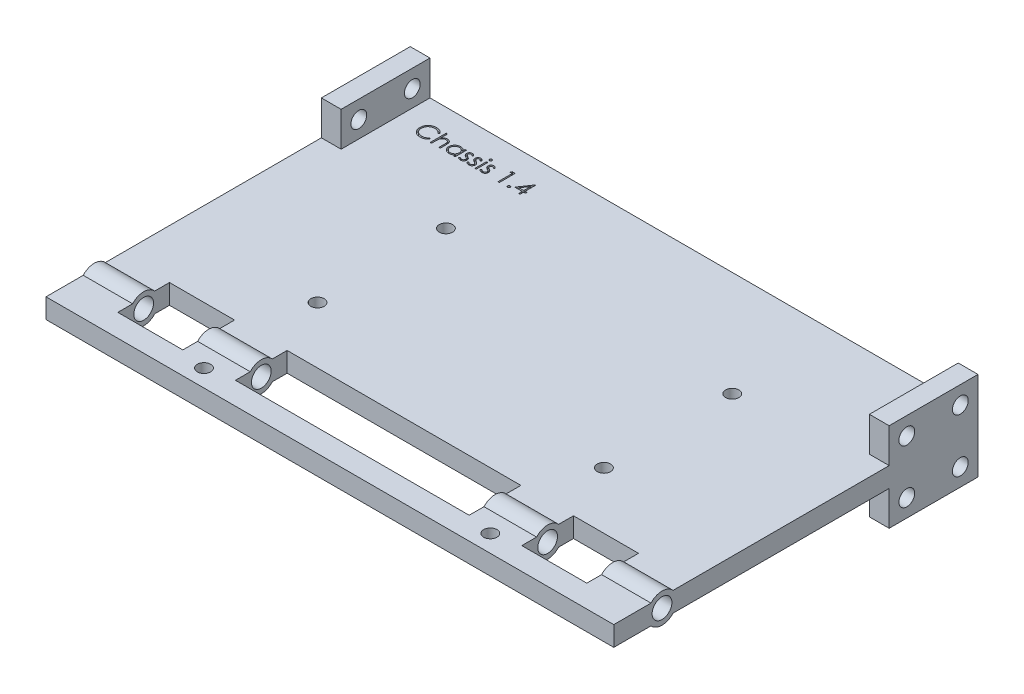
SolidWorks part; units mm, degrees
ref_plane "Front Plane" through (0, 0, 0) normal (0, 0, 1) x (1, 0, 0)
ref_plane "Top Plane" through (0, 0, 0) normal (0, 1, 0) x (1, 0, 0)
ref_plane "Right Plane" through (0, 0, 0) normal (1, 0, 0) x (0, 0, -1)
sketch "Sketch1" plane through (0, 0, 0) normal (0, 1, 0) x (1, 0, 0)
  line L0 (0, -36.8882) -> (115, -36.8882) construction
  line L1 (0, 0) -> (115, 0)
  line L2 (0, 0) -> (0, -73.7765)
  line L3 (0, -73.7765) -> (115, -73.7765)
  line L4 (115, 0) -> (115, -73.7765)
  line L5 (57.5, 0) -> (57.5, -73.7765) construction
  line L6 (57.5, -70.2765) -> (57.5, -73.7765) construction
  line L7 (28.5, -70.2765) -> (86.5, -70.2765) construction
  line L8 (28.5, -70.2765) -> (28.5, -47.2765) construction
  line L9 (28.5, -47.2765) -> (86.5, -47.2765) construction
  line L10 (86.5, -70.2765) -> (86.5, -47.2765) construction
  line L11 (28.5, -70.2765) -> (28.5, -21.2765) construction
  line L12 (28.5, -21.2765) -> (86.5, -21.2765) construction
  line L13 (86.5, -21.2765) -> (86.5, -70.2765) construction
  circle A0 centre (28.5, -47.2765) radius 1.35
  circle A1 centre (28.5, -70.2765) radius 1.35
  circle A2 centre (86.5, -47.2765) radius 1.35
  circle A3 centre (86.5, -70.2765) radius 1.35
  circle A4 centre (86.5, -21.2765) radius 1.35
  circle A5 centre (28.5, -21.2765) radius 1.35
  point P9 (57.5, 0)
  point P10 (57.5, -36.8882)
  point P14 (57.5, -47.2765)
  point P16 (57.5, -70.2765)
  dimension "D5" = 2.7
  dimension "D6" = 2.7
  dimension "D9" = 2.7
  dimension "D10" = 2.7
  dimension "D11" = 2.7
  dimension "D12" = 2.7
  dimension "D1" = 115
  dimension "D2" = 73.7765
  dimension "D3" = 23
  dimension "D4" = 58
  dimension "D7" = 3.5
  dimension "D8" = 49
extrude "Base Chassis" add sketch "Sketch1" along normal mid plane 4
sketch "Sketch14" plane through (0, 2, 0) normal (0, 1, 0) x (1, 0, 0)
  text T0 "Chassis 1.4"
extrude "Text" cut sketch "Sketch14" against normal blind 0.5
sketch "Sketch7" plane through (0, 0, 0) normal (-1, 0, 0) x (0, 0, 1)
  line L1 (0, 2) -> (0, -2) construction
  line L12 (0, -9) -> (0, 9)
  line L13 (0, 9) -> (18, 9)
  line L15 (0, -2) -> (73.7765, -2) construction
  line L23 (0, -9) -> (18, 9) construction
  line L24 (9, 0) -> (3.5828, 5.4172) construction
  line L28 (0, -9) -> (18, -9)
  line L35 (18, -9) -> (18, 9)
  circle A4 centre (9, 0) radius 7.661 construction
  circle A5 centre (3.5828, 5.4172) radius 1.6
  circle A9 centre (14.4172, 5.4172) radius 1.6
  circle A10 centre (14.4172, -5.4172) radius 1.6
  circle A11 centre (3.5828, -5.4172) radius 1.6
  point P1 (0, 0)
  point P2 (0, 0)
  point P24 (9, 0)
  dimension "D3" = 15.322
  dimension "D4" = 3.2
  dimension "D1" = 18
extrude "Mount Holes" add sketch "Sketch7" against normal blind 4
sketch "Sketch8" plane through (0, 0, 0) normal (-1, 0, 0) x (0, 0, 1)
  line L0 (9, 9) -> (9, -9) construction
  line L1 (18, 9) -> (0, 9) construction
  line L3 (64, 2) -> (64, -2) construction
  line L4 (18, 2) -> (73.7765, 2) construction
  line L5 (18, -2) -> (73.7765, -2) construction
  line L6 (9, 0) -> (64, 0) construction
  line L7 (0, -9) -> (18, -9) construction
  circle A0 centre (64, 0) radius 3
  dimension "D2" = 6
  dimension "D1" = 55
extrude "Shaft Extrude" add sketch "Sketch8" against normal through all
sketch "Sketch20" plane through (0, 0, 0) normal (-1, 0, 0) x (0, 0, 1)
  circle A0 centre (64, 0) radius 2
  dimension "D1" = 4
extrude "Shaft Cut" cut sketch "Sketch20" against normal through all
sketch "Sketch10" plane through (0, 2, 0) normal (0, 1, 0) x (1, 0, 0)
  line L0 (57.5, 0) -> (57.5, -73.7765) construction
  line L1 (115, 0) -> (4, 0) construction
  line L2 (0, -73.7765) -> (115, -73.7765) construction
  line L3 (0, -64) -> (57.5, -64) construction
  line L5 (10, -64) -> (10, -61.7639)
  line L11 (115, -73.7765) -> (115, -66.2361) construction
  line L19 (10, -61.7639) -> (10, -58.7639)
  line L20 (10, -58.7639) -> (23.1719, -58.7639)
  line L21 (23.1719, -58.7639) -> (23.1719, -61.7639)
  line L22 (23.1719, -61.7639) -> (23.1719, -64)
  line L23 (23.1719, -64) -> (23.1719, -66.2361)
  line L24 (23.1719, -69.2361) -> (33.8281, -69.2361) construction
  line L25 (23.1719, -66.2361) -> (23.1719, -69.2361)
  line L26 (23.1719, -69.2361) -> (10, -69.2361)
  line L27 (10, -69.2361) -> (10, -66.2361)
  line L28 (10, -66.2361) -> (10, -64)
  line L29 (0, -73.7765) -> (10, -73.7765) construction
  line L30 (10, -73.7765) -> (10, -69.2361) construction
  line L31 (23.1719, -58.7639) -> (33.8281, -58.7639) construction
  line L32 (33.8281, -58.7639) -> (33.8281, -61.7639)
  line L33 (33.8281, -61.7639) -> (33.8281, -64)
  line L34 (33.8281, -64) -> (33.8281, -66.2361)
  line L35 (33.8281, -66.2361) -> (33.8281, -69.2361)
  line L36 (33.8281, -69.2361) -> (57.5, -69.2361)
  line L37 (57.5, -69.2361) -> (57.5, -66.2361)
  line L38 (57.5, -66.2361) -> (57.5, -64)
  line L39 (57.5, -64) -> (57.5, -61.7639)
  line L40 (57.5, -61.7639) -> (57.5, -58.7639)
  line L41 (57.5, -58.7639) -> (33.8281, -58.7639)
  line L43 (115, -61.7639) -> (0, -61.7639) construction
  line L45 (0, -66.2361) -> (115, -66.2361) construction
  line L46 (0, -61.7639) -> (0, -66.2361) construction
  dimension "D1" = 3
  dimension "D2" = 3
  dimension "D3" = 10.6562
  dimension "D4" = 10
  dimension "D6" = 23.6719
extrude "Screw Hole" cut sketch "Sketch10" against normal through all both and the other way through all contours L40 L41 L32 L33 L34 L35 L36 L37 L38 L39 | L25 L26 L27 L28 L5 L19 L20 L21 L22 L23
ref_plane "Plane1" through (57.5, 0, 0) normal (1, 0, 0) x (0, 0, -1)
mirror "Mirror1" about plane through (57.5, 0, 0) normal (1, 0, 0) of "Screw Hole", "Mount Holes"
sketch "Sketch21" plane through (0, 2, 0) normal (0, 1, 0) x (1, 0, 0)
